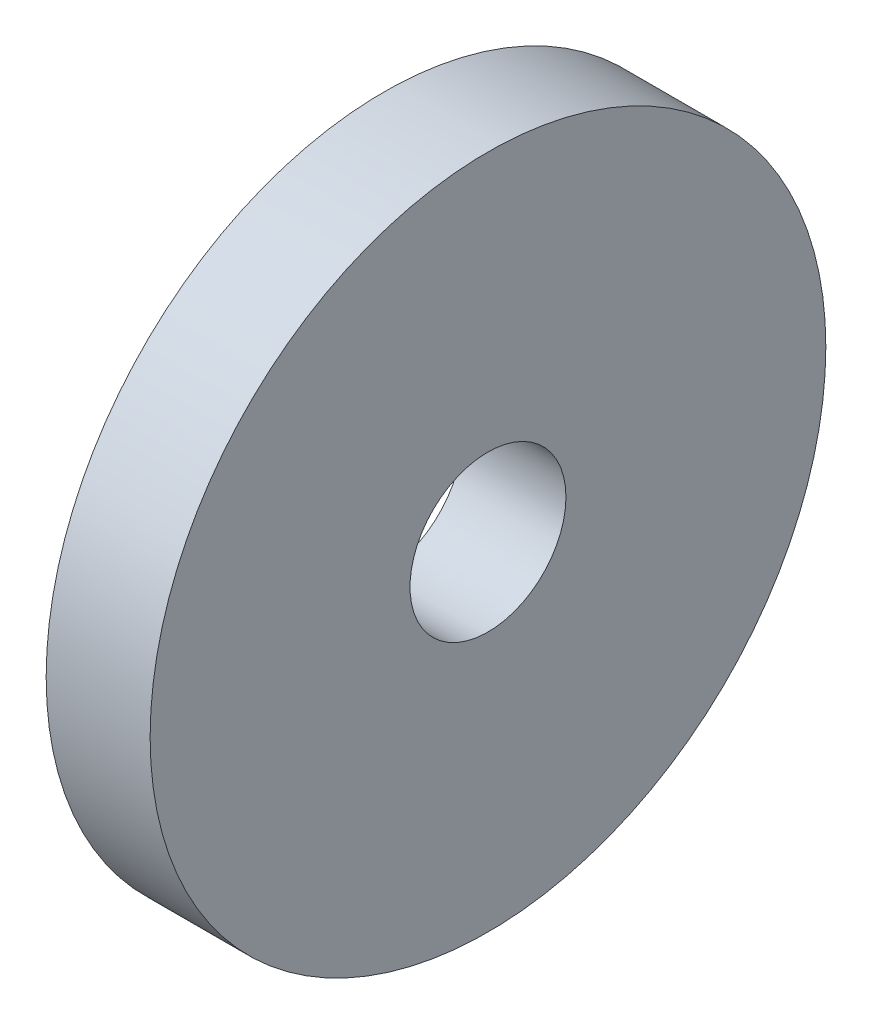
SolidWorks part; units mm, degrees
ref_plane "Alzado" through (0, 0, 0) normal (0, 0, 1) x (1, 0, 0)
ref_plane "Planta" through (0, 0, 0) normal (0, 1, 0) x (1, 0, 0)
ref_plane "Vista lateral" through (0, 0, 0) normal (1, 0, 0) x (0, 0, -1)
sketch "Croquis1" plane through (0, 0, 0) normal (1, 0, 0) x (0, 0, -1)
  circle A0 centre (0, 0) radius 1.5
  circle A1 centre (0, 0) radius 6.5
  dimension "D1" = 3
  dimension "D2" = 5
extrude "Saliente-Extruir1" add sketch "Croquis1" along normal blind 2
